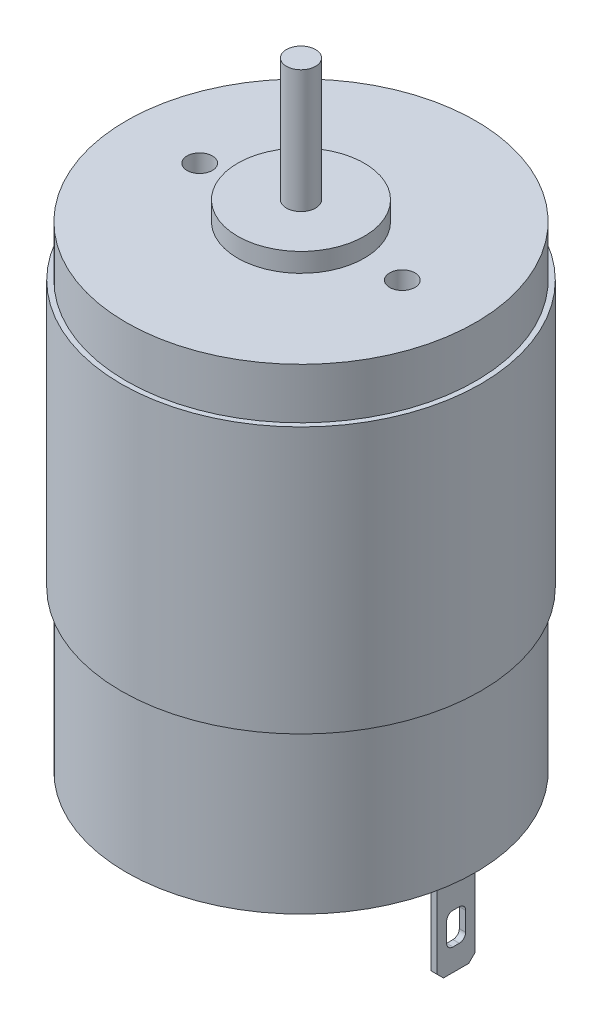
SolidWorks part; units mm, degrees
ref_plane "Front Plane" through (0, 0, 0) normal (0, 0, 1) x (1, 0, 0)
ref_plane "Top Plane" through (0, 0, 0) normal (0, 1, 0) x (1, 0, 0)
ref_plane "Right Plane" through (0, 0, 0) normal (1, 0, 0) x (0, 0, -1)
sketch "Sketch1" plane through (0, 0, 0) normal (0, 1, 0) x (1, 0, 0)
  circle A0 centre (0, 0) radius 13.8
  dimension "D1" = 27.6
extrude "Boss-Extrude1" add sketch "Sketch1" along normal blind 37.6
sketch "Sketch2" plane through (0, 37.6, 0) normal (0, 1, 0) x (1, 0, 0)
  circle A0 centre (0, 0) radius 5
  dimension "D1" = 10
extrude "Boss-Extrude2" add sketch "Sketch2" along normal blind 1.5
sketch "Sketch3" plane through (0, 39.1, 0) normal (0, 1, 0) x (1, 0, 0)
  circle A0 centre (0, 0) radius 1.15
  dimension "D1" = 2.3
extrude "Boss-Extrude3" add sketch "Sketch3" along normal blind 9.7
sketch "Sketch4" plane through (0, 37.6, 0) normal (0, 1, 0) x (1, 0, 0)
  line L0 (0, 0) -> (8, 0) construction
  line L1 (0, -15.18) -> (0, 15.18) construction
  circle A0 centre (8, 0) radius 1
  circle A1 centre (-8, 0) radius 1
  dimension "D2" = 2
  dimension "D1" = 8
extrude "Cut-Extrude1" cut sketch "Sketch4" against normal blind 5
sketch "Sketch5" plane through (0, 0, 0) normal (0, -1, 0) x (1, 0, 0)
  circle A0 centre (0, 0) radius 5
  dimension "D1" = 10
extrude "Boss-Extrude4" add sketch "Sketch5" along normal blind 2.5
sketch "Sketch6" plane through (0, 0, 0) normal (0, -1, 0) x (1, 0, 0)
  line L0 (0, 0) -> (12, 0) construction
  line L1 (0, -15.18) -> (0, 15.18) construction
  line L2 (11.75, 1.5) -> (12.25, 1.5)
  line L3 (11.75, 1.5) -> (11.75, -1.5)
  line L4 (11.75, -1.5) -> (12.25, -1.5)
  line L5 (12.25, 1.5) -> (12.25, -1.5)
  line L6 (11.75, 1.5) -> (12.25, -1.5) construction
  line L7 (11.75, -1.5) -> (12.25, 1.5) construction
  line L8 (-11.75, -1.5) -> (-12.25, -1.5)
  line L9 (-12.25, 1.5) -> (-12.25, -1.5)
  line L10 (-11.75, 1.5) -> (-12.25, 1.5)
  line L11 (-11.75, 1.5) -> (-11.75, -1.5)
  line L12 (-11.75, -1.5) -> (-12.25, 1.5) construction
  line L13 (-11.75, 1.5) -> (-12.25, -1.5) construction
  point P13 (-12, 0)
  dimension "D1" = 12
  dimension "D2" = 3
  dimension "D3" = 0.5
extrude "Boss-Extrude5" add sketch "Sketch6" along normal blind 7.5
sketch "Sketch7" plane through (12.25, 0, 0) normal (1, 0, 0) x (0, 0, -1)
  line L0 (0, -7.5) -> (0, -4.5) construction
  line L1 (1.5, -7.5) -> (-1.5, -7.5) construction
  line L3 (-0.75, -3.25) -> (0.75, -3.25)
  line L4 (-0.75, -3.25) -> (-0.75, -5.75)
  line L5 (-0.75, -5.75) -> (0.75, -5.75)
  line L6 (0.75, -3.25) -> (0.75, -5.75)
  line L7 (-0.75, -3.25) -> (0.75, -5.75) construction
  line L8 (-0.75, -5.75) -> (0.75, -3.25) construction
  dimension "D1" = 3
  dimension "D2" = 2.5
  dimension "D3" = 1.5
extrude "Cut-Extrude2" cut sketch "Sketch7" against normal up to surface (24.5 mm away) up to face at (-12.25, -3.75, 0)
chamfer "Chamfer1" distance 0.5 angle 45 4 edges at (-12, -7.5, -1.5) (-12, -7.5, 1.5) (12, -7.5, -1.5) (12, -7.5, 1.5)
fillet "Fillet1" radius 0.5 8 edges at (-12, -5.75, 0.75) (-12, -5.75, -0.75) (-12, -3.25, -0.75) (-12, -3.25, 0.75) (12, -3.25, 0.75) (12, -5.75, 0.75) (12, -3.25, -0.75) (12, -5.75, -0.75)
ref_plane "Plane1" through (0, 33.6, 0) normal (0, 1, 0) x (1, 0, 0)
sketch "Sketch8" plane through (0, 33.6, 0) normal (0, 1, 0) x (1, 0, 0)
  circle A0 centre (0, 0) radius 13.8
  circle A1 centre (0, 0) radius 14.2
  dimension "D1" = 28.4
extrude "Boss-Extrude6" add sketch "Sketch8" against normal blind 21
